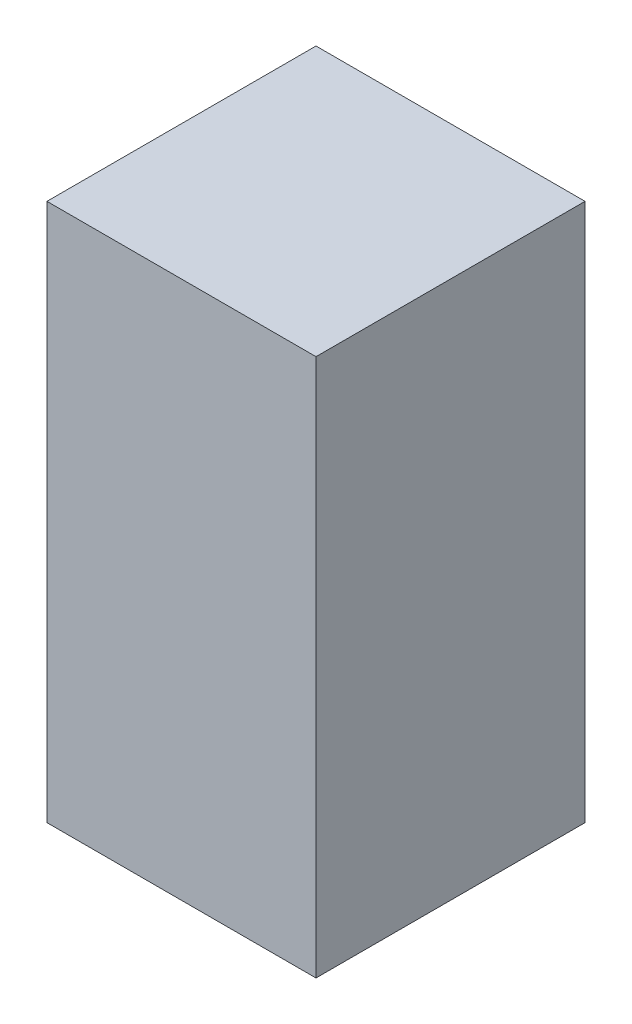
SolidWorks part; units mm, degrees
ref_plane "Front Plane" through (0, 0, 0) normal (0, 0, 1) x (1, 0, 0)
ref_plane "Top Plane" through (0, 0, 0) normal (0, 1, 0) x (1, 0, 0)
ref_plane "Right Plane" through (0, 0, 0) normal (1, 0, 0) x (0, 0, -1)
sketch "Sketch1" plane through (0, 0, 0) normal (0, 1, 0) x (1, 0, 0)
  line L0 (-2.7586, 3.3333) -> (-2.7586, -6.6667)
  line L1 (-2.7586, -6.6667) -> (7.2414, -6.6667)
  line L2 (7.2414, -6.6667) -> (7.2414, 3.3333)
  line L3 (7.2414, 3.3333) -> (-2.7586, 3.3333)
  dimension "D1" = 10
  dimension "D2" = 10
extrude "Boss-Extrude1" add sketch "Sketch1" along normal blind 20
